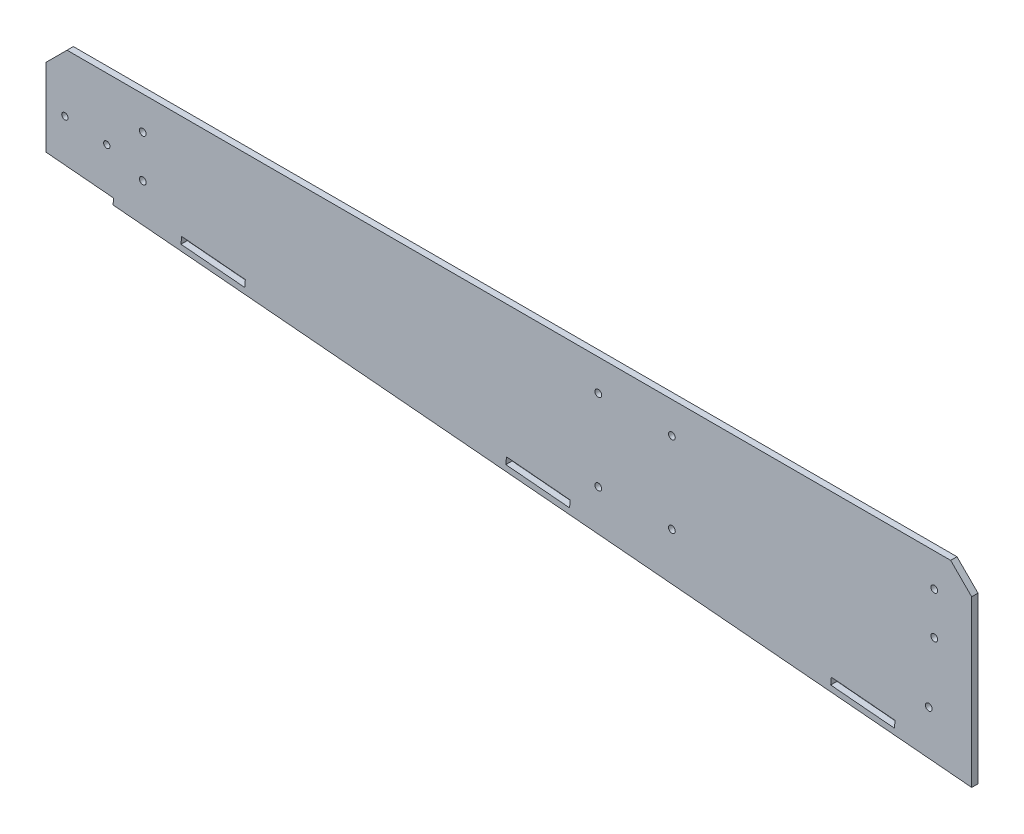
SolidWorks part; units mm, degrees
material "Acrylic (Medium-high impact)"
ref_plane "前视基准面" through (0, 0, 0) normal (0, 0, 1) x (1, 0, 0)
ref_plane "上视基准面" through (0, 0, 0) normal (0, 1, 0) x (1, 0, 0)
ref_plane "右视基准面" through (0, 0, 0) normal (1, 0, 0) x (0, 0, -1)
sketch "草图1" plane through (0, 0, 0) normal (0, 0, 1) x (1, 0, 0)
  line L0 (-31.7701, 71.7677) -> (408.2299, 71.7677)
  line L1 (408.2299, 71.7677) -> (408.2299, -16.7273)
  line L2 (408.2299, -16.7273) -> (-31.7701, 21.7677)
  line L3 (-31.7701, 21.7677) -> (-31.7701, 71.7677)
  dimension "D2" = 440
  dimension "D3" = 50
  dimension "D4" = 5
extrude "凸台-拉伸1" add sketch "草图1" along normal blind 3
sketch "草图3" plane through (0, 0, 3) normal (0, 0, 1) x (1, 0, 0)
  line L0 (0.1081, 18.9787) -> (0.3696, 21.9673)
  line L1 (-31.7701, 21.7677) -> (408.2299, -16.7273) construction
  line L2 (0.3696, 21.9673) -> (-31.7701, 24.7792)
  line L3 (-31.7701, 71.7677) -> (-31.7701, 21.7677) construction
  line L4 (-31.7701, 24.7792) -> (-31.7701, 21.7677)
  line L5 (-31.7701, 21.7677) -> (0.1081, 18.9787)
  line L6 (371.7923, -7.3158) -> (371.496, -10.7028)
  line L7 (371.7923, -7.3158) -> (341.508, -4.6662)
  line L8 (371.496, -10.7028) -> (341.2117, -8.0533)
  line L9 (341.508, -4.6662) -> (341.2117, -8.0533)
  line L10 (371.5757, -7.4976) -> (371.3142, -10.4861) construction
  line L11 (341.6898, -4.8829) -> (341.4284, -7.8715) construction
  line L12 (371.5757, -7.4976) -> (341.6898, -4.8829) construction
  line L13 (371.3142, -10.4861) -> (341.4284, -7.8715) construction
  line L14 (217.3822, 6.1934) -> (217.0858, 2.8063)
  line L15 (217.3822, 6.1934) -> (187.0978, 8.8429)
  line L16 (217.0858, 2.8063) -> (186.8015, 5.4559)
  line L17 (187.0978, 8.8429) -> (186.8015, 5.4559)
  line L18 (62.972, 19.7025) -> (62.6756, 16.3155)
  line L19 (62.972, 19.7025) -> (32.6877, 22.3521)
  line L20 (62.6756, 16.3155) -> (32.3913, 18.965)
  line L21 (32.6877, 22.3521) -> (32.3913, 18.965)
  dimension "D2" = 0.2
  dimension "D3" = 0.2
  dimension "D1" = 0.2
  dimension "D4" = 3
  dimension "D5" = 32
  dimension "D6" = 0.2
  dimension "D7" = 3
extrude "切除-拉伸2" cut sketch "草图3" against normal blind 10
sketch "Sketch1" plane through (0, 0, 0) normal (0, 0, -1) x (-1, 0, 0)
  circle A0 centre (22.7922, 44.0701) radius 1.5 construction
  circle A1 centre (2.8683, 42.327) radius 1.5 construction
  circle A7 centre (22.7922, 44.0701) radius 1.5
  circle A8 centre (2.8683, 42.327) radius 1.5
  circle A9 centre (-230.7299, 56.7835) radius 1.6
  circle A10 centre (-230.7299, 18.278) radius 1.6
  circle A11 centre (-265.7299, 18.278) radius 1.6
  circle A15 centre (-265.7299, 56.7835) radius 1.6
  point P1 (-265.7299, 56.7835)
extrude "Cut-Extrude2" cut sketch "Sketch1" against normal blind 3
chamfer "Chamfer1" distance 10 angle 45 2 edges at (-31.7701, 71.7677, 1.5) (408.2299, 71.7677, 1.5)
sketch "Sketch2" plane through (0, 0, 0) normal (0, 0, -1) x (-1, 0, 0)
  circle A0 centre (-390.4406, 36.0239) radius 1.6
  circle A1 centre (-387.8259, 6.138) radius 1.6
extrude "Cut-Extrude3" cut sketch "Sketch2" against normal blind 10
sketch "Sketch3" plane through (0, 0, 0) normal (0, 0, -1) x (-1, 0, 0)
  circle A0 centre (-390.4406, 56.0239) radius 1.6 construction
  circle A1 centre (-14.2299, 36.0239) radius 1.6 construction
  circle A2 centre (-14.2299, 56.0239) radius 1.6 construction
  circle A3 centre (-390.4406, 56.0239) radius 1.6
  circle A4 centre (-14.2299, 36.0239) radius 1.6
  circle A5 centre (-14.2299, 56.0239) radius 1.6
extrude "Cut-Extrude4" cut sketch "Sketch3" against normal blind 39
